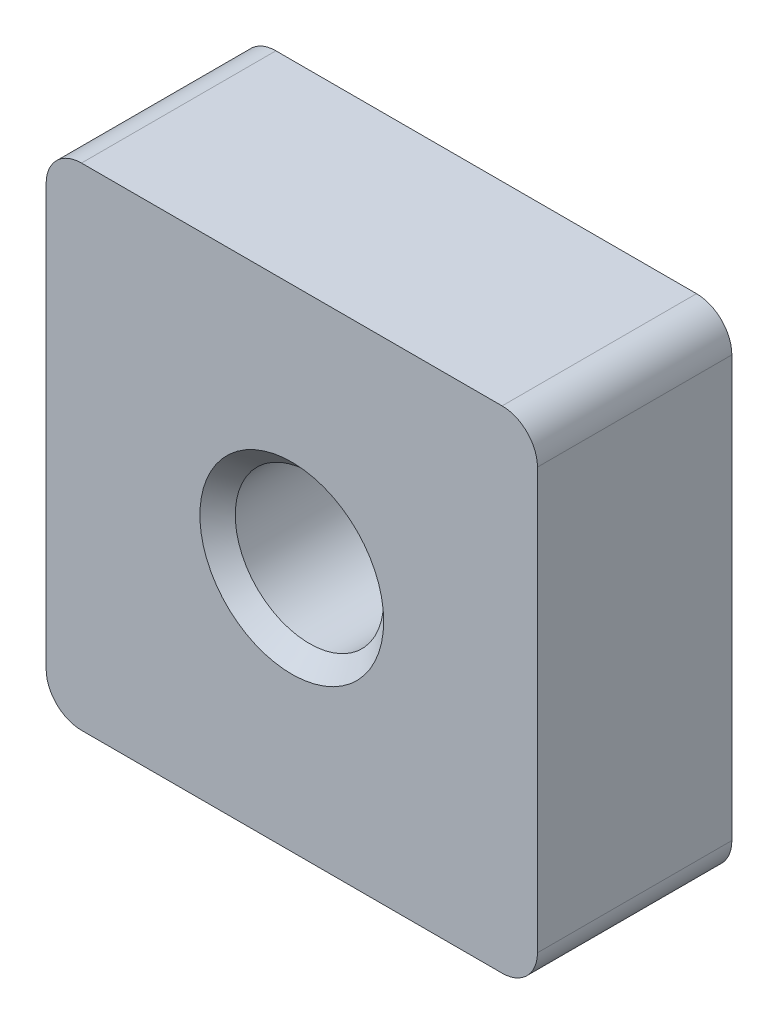
SolidWorks part; units mm, degrees
ref_plane "Спереди" through (0, 0, 0) normal (0, 0, 1) x (1, 0, 0)
ref_plane "Сверху" through (0, 0, 0) normal (0, 1, 0) x (1, 0, 0)
ref_plane "Справа" through (0, 0, 0) normal (1, 0, 0) x (0, 0, -1)
sketch "Эскиз1" plane through (0, 0, 0) normal (0, 0, 1) x (1, 0, 0)
  line L1 (-6.95, -6.95) -> (6.95, -6.95)
  line L2 (-6.95, -6.95) -> (-6.95, 6.95)
  line L3 (-6.95, 6.95) -> (6.95, 6.95)
  line L4 (6.95, -6.95) -> (6.95, 6.95)
  line L5 (-6.95, -6.95) -> (6.95, 6.95) construction
  line L6 (-6.95, 6.95) -> (6.95, -6.95) construction
  point P0 (0, 0)
  dimension "D1" = 13.9
extrude "Бобышка-Вытянуть1" add sketch "Эскиз1" along normal blind 5.5
hole_wizard "Отверстие обработанное метчиком M52" positions "Эскиз2" profile "Эскиз3" tap size "M5" standard "ISO" end condition through all
sketch "Эскиз2" plane through (0, 0, 5.5) normal (0, 0, 1) x (1, 0, 0)
  point P0 (0, 0)
sketch "Эскиз3" plane through (0, 0, 5.5) normal (1, 0, 0) x (0, -1, 0)
  line L0 (0, 0) -> (0, 5.5)
  line L1 (0, 5.5) -> (2.6, 5.5)
  line L2 (2.1, 5) -> (2.1, 0.5)
  line L3 (2.1, 0.5) -> (2.6, 0)
  line L5 (2.6, 0) -> (0, 0)
  line L6 (-2.1, 0.5) -> (-2.6, 0) construction
  line L7 (2.6, 5.5) -> (2.1, 5)
  line L8 (-2.6, 5.5) -> (-2.1, 5) construction
  line L11 (0, -6.35) -> (0, 107.95) construction
  dimension "Диаметр проходного сверла" = 4.2
  dimension "Глубина проходного сверла" = 5.5
  dimension "Диаметр передней зенковки" = 5.2
  dimension "Угол передней зенковки" = 90
  dimension "Диаметр задней зенковки" = 5.2
  dimension "Угол задней зенковки" = 90
cosmetic thread "Отверстие резьбы1" parameters "D2"=5
fillet "Скругление1" radius 1 4 edges at (6.95, 6.95, 2.75) (-6.95, 6.95, 2.75) (6.95, -6.95, 2.75) (-6.95, -6.95, 2.75)
